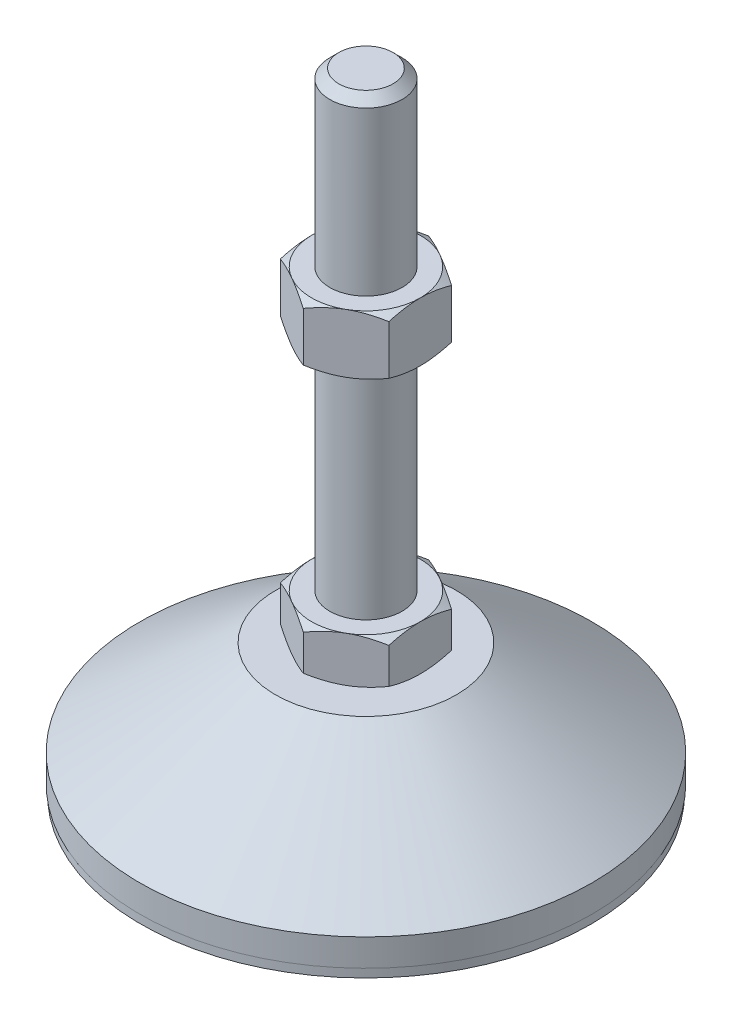
SolidWorks part; units mm, degrees
ref_plane "Спереди" through (0, 0, 0) normal (0, 0, 1) x (1, 0, 0)
ref_plane "Сверху" through (0, 0, 0) normal (0, 1, 0) x (1, 0, 0)
ref_plane "Справа" through (0, 0, 0) normal (1, 0, 0) x (0, 0, -1)
sketch "Эскиз1" plane through (0, 0, 0) normal (0, 0, 1) x (1, 0, 0)
  line L0 (0, 0) -> (-49.8, 0)
  line L1 (-49.8, 0) -> (-49.8, 2)
  line L2 (-49.8, 2) -> (-50, 2)
  line L3 (-50, 2) -> (-50, 8)
  line L4 (-50, 8) -> (-20, 29)
  line L5 (-20, 29) -> (-8, 29)
  line L12 (-8, 39) -> (-8, 137)
  line L13 (-8, 137) -> (-6, 139)
  line L14 (-6, 139) -> (0, 139)
  line L15 (0, 139) -> (0, 0) construction
  line L16 (-8, 29) -> (0, 29) construction
  line L17 (0, 0) -> (0, 139)
  line L18 (0, 0) -> (0, -7.9595) construction
  line L19 (-8, 39) -> (-8, 29)
  point P8 (-8, 88)
  point P23 (-14, 29)
  dimension "D1" = 16
  dimension "D2" = 29
  dimension "D3" = 10
  dimension "D4" = 100
  dimension "D5" = 8
  dimension "D6" = 2
  dimension "D7" = 45
  dimension "D8" = 40
  dimension "D9" = 2
  dimension "D10" = 100
  dimension "D11" = 6
  dimension "D12" = 0.2
revolve "Повернуть1" add sketch "Эскиз1" angle 360 about L17
sketch "Эскиз2" plane through (0, 29, 0) normal (0, 1, 0) x (1, 0, 0)
  line L1 (0, 13.8564) -> (-12, 6.9282)
  line L2 (-12, 6.9282) -> (-12, -6.9282)
  line L3 (-12, -6.9282) -> (0, -13.8564)
  line L4 (0, -13.8564) -> (12, -6.9282)
  line L5 (12, -6.9282) -> (12, 6.9282)
  line L6 (12, 6.9282) -> (0, 13.8564)
  circle A0 centre (0, 0) radius 12 construction
  dimension "D1" = 24
extrude "Бобышка-Вытянуть1" add sketch "Эскиз2" along normal up to vertex (10 mm away) up to point (-8, 39, 0)
ref_plane "Плоскость1" through (0, 88, 0) normal (0, 1, 0) x (1, 0, 0)
sketch "Эскиз3" plane through (0, 88, 0) normal (0, 1, 0) x (1, 0, 0)
  line L6 (12, 6.9282) -> (0, 13.8564)
  line L7 (0, 13.8564) -> (-12, 6.9282)
  line L8 (-12, 6.9282) -> (-12, -6.9282)
  line L9 (-12, -6.9282) -> (0, -13.8564)
  line L10 (0, -13.8564) -> (12, -6.9282)
  line L11 (12, -6.9282) -> (12, 6.9282)
  line L12 (12, 6.9282) -> (0, 13.8564)
  line L13 (0, 13.8564) -> (-12, 6.9282)
  line L14 (-12, 6.9282) -> (-12, -6.9282)
  line L15 (-12, -6.9282) -> (0, -13.8564)
  line L16 (0, -13.8564) -> (12, -6.9282)
  line L17 (12, -6.9282) -> (12, 6.9282)
  dimension "D1" = 0
extrude "Бобышка-Вытянуть2" add sketch "Эскиз3" along normal blind 13
sketch "Эскиз4" plane through (0, 0, 0) normal (0, 0, 1) x (1, 0, 0)
  line L0 (-12, 101) -> (-23.2583, 94.5)
  line L1 (-23.2583, 94.5) -> (-23.2583, 101)
  line L2 (-23.2583, 101) -> (-12, 101)
  line L3 (-23.2583, 94.5) -> (-12, 88)
  line L4 (50, 88) -> (-50, 88) construction
  line L5 (-12, 88) -> (-23.2583, 88)
  line L6 (-23.2583, 88) -> (-23.2583, 94.5)
  line L7 (-12, 101) -> (-12, 88) construction
  line L8 (-12, 39) -> (-20.6603, 39)
  line L9 (-20.6603, 39) -> (-20.6603, 34)
  line L10 (-20.6603, 34) -> (-12, 39)
  line L11 (-12, 29) -> (-20.6603, 34)
  line L12 (-20.6603, 34) -> (-20.6603, 29)
  line L13 (-20.6603, 29) -> (-12, 29)
  line L14 (0, 139) -> (0, 96.3793) construction
  dimension "D1" = 30
  dimension "D2" = 30
revolve "Вырез-Повернуть2" cut sketch "Эскиз4" angle 360 about L14
